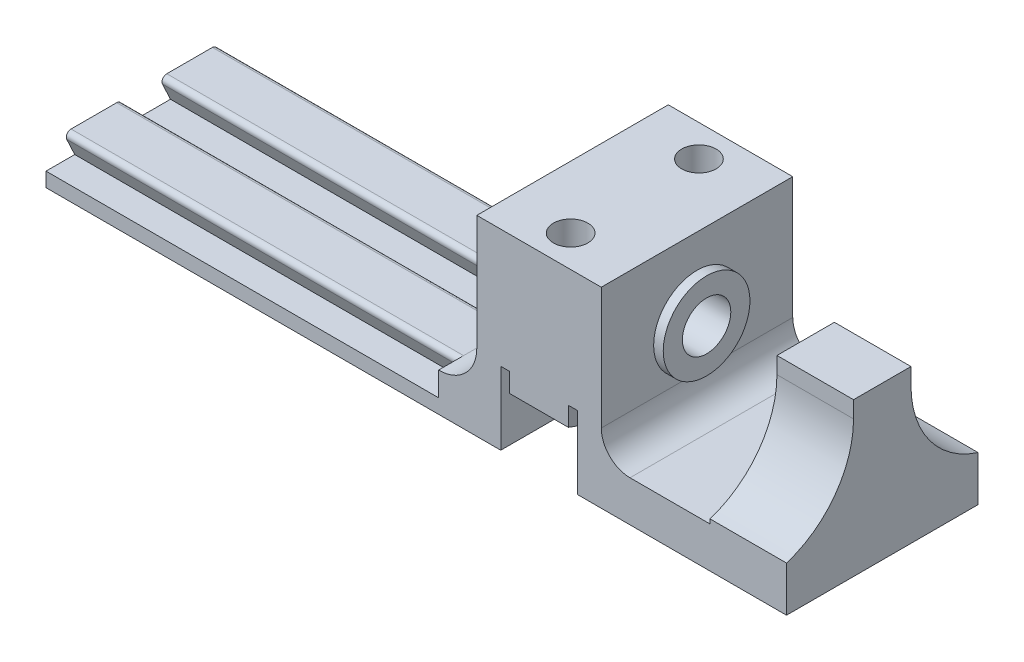
SolidWorks part; units mm, degrees
ref_plane "Front Plane" through (0, 0, 0) normal (0, 0, 1) x (1, 0, 0)
ref_plane "Top Plane" through (0, 0, 0) normal (0, 1, 0) x (1, 0, 0)
ref_plane "Right Plane" through (0, 0, 0) normal (1, 0, 0) x (0, 0, -1)
sketch "Sketch1" plane through (0, 0, 0) normal (0, 1, 0) x (1, 0, 0)
  line L1 (-29, -40) -> (29, -40)
  line L2 (-29, -40) -> (-29, 40)
  line L3 (-29, 40) -> (29, 40)
  line L4 (29, -40) -> (29, 40)
  line L5 (-29, -40) -> (29, 40) construction
  line L6 (-29, 40) -> (29, -40) construction
  point P0 (0, 0)
  dimension "D1" = 58
  dimension "D2" = 80
extrude "Boss-Extrude1" add sketch "Sketch1" along normal blind 4
sketch "Sketch2" plane through (-29, 0, 0) normal (-1, 0, 0) x (0, 0, 1)
  line L10 (0, 0) -> (0, 4) construction
  line L12 (-40, 4) -> (40, 4) construction
  line L13 (1.8342, 4) -> (-1.8342, 4)
  line L14 (-1.8342, 4) -> (-3, 1.5)
  line L15 (-3, 1.5) -> (3, 1.5)
  line L16 (1.8342, 4) -> (3, 1.5)
  line L17 (40, 4) -> (40, 0) construction
  line L18 (8.1658, 4) -> (11.8342, 4)
  line L19 (11.8342, 4) -> (13, 1.5)
  line L20 (13, 1.5) -> (7, 1.5)
  line L21 (7, 1.5) -> (8.1658, 4)
  line L22 (10, 4) -> (10, 1.5) construction
  line L23 (-10, 4) -> (-10, 1.5) construction
  line L24 (-7, 1.5) -> (-8.1658, 4)
  line L25 (-13, 1.5) -> (-7, 1.5)
  line L26 (-11.8342, 4) -> (-13, 1.5)
  line L27 (-8.1658, 4) -> (-11.8342, 4)
  point P6 (0, 1.5)
  dimension "D1" = 65
  dimension "D2" = 2.5
  dimension "D3" = 6
  dimension "D4" = 20
extrude "Cut-Extrude1" cut sketch "Sketch2" against normal blind 25
sketch "Sketch5" plane through (0, 0, 40) normal (0, 0, 1) x (1, 0, 0)
  line L0 (-4, 4) -> (-29, 4) construction
  line L1 (29, 4) -> (16, 4)
  line L2 (29, 4) -> (29, 20)
  line L3 (29, 20) -> (16, 20)
  line L4 (16, 4) -> (16, 20)
  line L5 (-4, 4) -> (-29, 4) construction
  line L6 (-29, 0) -> (29, 0) construction
  dimension "D1" = 20
  dimension "D2" = 20
extrude "Boss-Extrude3" add sketch "Sketch5" against normal up to surface (80 mm away) up to face at (0, 2, -40)
sketch "Sketch6" plane through (29, 0, 0) normal (1, 0, 0) x (0, 0, -1)
  line L0 (0, 20) -> (0, 4) construction
  line L1 (40, 20) -> (-40, 20) construction
  line L3 (40, 4) -> (-40, 4) construction
  line L4 (40, 4) -> (-40, 4) construction
  circle A0 centre (0, 12) radius 2.53
  dimension "D1" = 5.06
extrude "Cut-Extrude2" cut sketch "Sketch6" against normal through all
sketch "Sketch7" plane through (29, 0, 0) normal (1, 0, 0) x (0, 0, -1)
  circle A0 centre (0, 12) radius 2.53 construction
  circle A1 centre (0, 12) radius 2.53
  circle A2 centre (0, 12) radius 4.53
  dimension "D1" = 2
extrude "Boss-Extrude4" add sketch "Sketch7" along normal blind 1
sketch "Sketch8" plane through (0, 20, 0) normal (0, 1, 0) x (1, 0, 0)
  line L0 (22.5, 40) -> (22.5, -40) construction
  line L1 (16, 40) -> (29, 40) construction
  line L2 (29, -40) -> (16, -40) construction
  line L4 (16, 40) -> (16, -40) construction
  line L5 (16, -6.7) -> (22.5, -6.7) construction
  line L6 (22.5, -6.7) -> (16, 6.7) construction
  line L7 (16, 6.7) -> (22.5, 6.7) construction
  line L8 (22.5, 8.5) -> (29, 8.5) construction
  line L9 (17.9973, 36) -> (22.5, 36) construction
  line L10 (29, 40) -> (29, -40) construction
  line L11 (29, 8.5) -> (29, -8.5) construction
  line L12 (16, 6.7) -> (16, -6.7) construction
  line L13 (29, -8.5) -> (22.5, -8.5) construction
  line L14 (29, 10) -> (16, 10) construction
  line L16 (16, -10) -> (29, -10) construction
  line L17 (22.5, -8.5) -> (22.5, -10) construction
  line L18 (29, -8.5) -> (29, -10) construction
  line L19 (29, -10) -> (29, 8.5) construction
  line L20 (29, 8.5) -> (29, 10) construction
  circle A1 centre (22.5, 6.7) radius 1.8
  circle A2 centre (22.5, -6.7) radius 1.8
  point P14 (16, 0)
  point P15 (16, 0)
  dimension "D1" = 3.6
  dimension "D2" = 1.5
  dimension "D3" = 20
extrude "Cut-Extrude3" cut sketch "Sketch8" against normal through all
sketch "Sketch9" plane through (0, 0, 0) normal (0, -1, 0) x (1, 0, 0)
  line L0 (-29, 40) -> (29, 40) construction
  line L1 (18.5, 40) -> (26.5, 40)
  line L2 (18.5, 40) -> (18.5, -40)
  line L3 (18.5, -40) -> (26.5, -40)
  line L4 (26.5, 40) -> (26.5, -40)
  line L5 (29, -40) -> (-29, -40) construction
  line L6 (22.5, 36) -> (22.5, 40) construction
  line L7 (29, 40) -> (29, -40) construction
  dimension "D1" = 8
extrude "Cut-Extrude4" cut sketch "Sketch9" against normal blind 7.6
sketch "Sketch13" plane through (29, 0, 0) normal (1, 0, 0) x (0, 0, -1)
  line L0 (-40, 0) -> (40, 0) construction
  line L1 (0, 5.8719) -> (0, 12) construction
  line L2 (-3, 0) -> (3, 0)
  line L3 (-3, 0) -> (-3, 4.261)
  line L4 (-3, 4.261) -> (3, 4.261)
  line L5 (3, 0) -> (3, 4.261)
  circle A1 centre (0, 12) radius 7.239 construction
  circle A2 centre (0, 12) radius 7.739 construction
  point P10 (0, 0)
  dimension "D1" = 0.5
  dimension "D2" = 6
extrude "Boss-Extrude6" add sketch "Sketch13" along normal blind 11.35
sketch "Sketch14" plane through (40.35, 0, 0) normal (1, 0, 0) x (0, 0, -1)
  line L0 (3, 0) -> (3, 4.261) construction
  line L1 (-3, 0) -> (3, 0)
  line L2 (-3, 0) -> (-3, 16)
  line L3 (-3, 16) -> (3, 16)
  line L4 (3, 0) -> (3, 16)
  dimension "D1" = 16
extrude "Boss-Extrude7" add sketch "Sketch14" along normal blind 8
sketch "Sketch15" plane through (29, 0, 0) normal (1, 0, 0) x (0, 0, -1)
  line L0 (-40, 0) -> (-3, 0) construction
  line L1 (-20, 0) -> (20, 0)
  line L2 (-20, 0) -> (-20, 4.261)
  line L3 (-20, 4.261) -> (20, 4.261)
  line L4 (20, 0) -> (20, 4.261)
  line L5 (3, 4.261) -> (-3, 4.261) construction
  point P6 (0, 0)
  dimension "D1" = 40
extrude "Boss-Extrude8" add sketch "Sketch15" along normal up to surface (19.35 mm away) up to face at (48.35, 8, 0)
fillet "Fillet1" radius 10 2 edges at (44.35, 4.261, 3) (44.35, 4.261, -3)
fillet "Fillet2" radius 3 1 edges at (29, 4.261, 0)
fillet "Fillet3" radius 3 2 edges at (29, 3.6305, -20) (29, 3.6305, 20)
sketch "Sketch17" plane through (0, 4, 0) normal (0, 1, 0) x (1, 0, 0)
  line L1 (-1, -36) -> (16, -36)
  line L2 (-1, -36) -> (-1, -12)
  line L3 (-1, -12) -> (16, -12)
  line L4 (16, -36) -> (16, -12)
  line L5 (16, 40) -> (16, -40) construction
  line L6 (0, 0) -> (11.9578, 0) construction
  line L7 (-1, 12) -> (16, 12)
  line L8 (16, 36) -> (16, 12)
  line L9 (-1, 36) -> (16, 36)
  line L10 (-1, 36) -> (-1, 12)
  line L11 (-29, -40) -> (16, -40) construction
  line L12 (-4, -11.8342) -> (-4, -8.1658) construction
  dimension "D1" = 4
  dimension "D2" = 12
  dimension "D3" = 3
extrude "Cut-Extrude6" cut sketch "Sketch17" against normal through all
fillet "Fillet4" radius 14 2 edges at (16, 4, -38) (16, 4, 38)
fillet "Fillet5" radius 4 1 edges at (16, 4, 0)
fillet "Fillet6" radius 2 4 edges at (16, 9, 36) (16, 4, 12) (16, 4, -12) (16, 9, -36)
fillet "Fillet7" radius 0.5 6 edges at (-16.5, 4, 11.8342) (-16.5, 4, 8.1658) (-16.5, 4, 1.8342) (-16.5, 4, -1.8342) (-16.5, 4, -8.1658) (-16.5, 4, -11.8342)
sketch "Sketch18" plane through (0, 7.6, 0) normal (0, -1, 0) x (1, 0, 0)
  line L0 (20.8828, 38.8011) -> (24.1172, 38.8011)
  line L1 (24.1172, 38.8011) -> (25.7344, 36)
  line L2 (25.7344, 36) -> (24.1172, 33.1989)
  line L3 (24.1172, 33.1989) -> (20.8828, 33.1989)
  line L4 (20.8828, 33.1989) -> (19.2656, 36)
  line L5 (19.2656, 36) -> (20.8828, 38.8011)
  line L6 (20.8828, 38.8011) -> (20.8828, 33.1989) construction
  line L7 (20.8828, 33.1989) -> (25.7344, 36) construction
  line L8 (19.2656, 36) -> (25.7344, 36) construction
  line L9 (20.8828, 9.5011) -> (24.1172, 9.5011)
  line L10 (24.1172, 9.5011) -> (25.7344, 6.7)
  line L11 (25.7344, 6.7) -> (24.1172, 3.8989)
  line L12 (24.1172, 3.8989) -> (20.8828, 3.8989)
  line L13 (20.8828, 3.8989) -> (19.2656, 6.7)
  line L14 (19.2656, 6.7) -> (20.8828, 9.5011)
  line L15 (20.8828, 9.5011) -> (20.8828, 3.8989) construction
  line L16 (20.8828, 3.8989) -> (25.7344, 6.7) construction
  line L17 (19.2656, 6.7) -> (25.7344, 6.7) construction
  line L18 (20.8828, -3.8989) -> (24.1172, -3.8989)
  line L19 (24.1172, -3.8989) -> (25.7344, -6.7)
  line L20 (25.7344, -6.7) -> (24.1172, -9.5011)
  line L21 (24.1172, -9.5011) -> (20.8828, -9.5011)
  line L22 (20.8828, -9.5011) -> (19.2656, -6.7)
  line L23 (19.2656, -6.7) -> (20.8828, -3.8989)
  line L24 (20.8828, -3.8989) -> (20.8828, -9.5011) construction
  line L25 (20.8828, -9.5011) -> (25.7344, -6.7) construction
  line L26 (19.2656, -6.7) -> (25.7344, -6.7) construction
  line L27 (20.8828, -33.1989) -> (24.1172, -33.1989)
  line L28 (24.1172, -33.1989) -> (25.7344, -36)
  line L29 (25.7344, -36) -> (24.1172, -38.8011)
  line L30 (24.1172, -38.8011) -> (20.8828, -38.8011)
  line L31 (20.8828, -38.8011) -> (19.2656, -36)
  line L32 (19.2656, -36) -> (20.8828, -33.1989)
  line L33 (20.8828, -33.1989) -> (20.8828, -38.8011) construction
  line L34 (20.8828, -38.8011) -> (25.7344, -36) construction
  line L35 (19.2656, -36) -> (25.7344, -36) construction
  line L36 (20.0168, 40.3011) -> (24.9832, 40.3011)
  line L37 (24.9832, 40.3011) -> (27.4665, 36)
  line L38 (27.4665, 36) -> (24.9832, 31.6989)
  line L39 (24.9832, 31.6989) -> (20.0168, 31.6989)
  line L40 (20.0168, 31.6989) -> (17.5335, 36)
  line L41 (17.5335, 36) -> (20.0168, 40.3011)
  line L42 (20.0168, 11.0011) -> (24.9832, 11.0011)
  line L43 (24.9832, 11.0011) -> (27.4665, 6.7)
  line L44 (27.4665, 6.7) -> (24.9832, 2.3989)
  line L45 (24.9832, 2.3989) -> (20.0168, 2.3989)
  line L46 (20.0168, 2.3989) -> (17.5335, 6.7)
  line L47 (17.5335, 6.7) -> (20.0168, 11.0011)
  line L48 (20.0168, -2.3989) -> (24.9832, -2.3989)
  line L49 (24.9832, -2.3989) -> (27.4665, -6.7)
  line L50 (27.4665, -6.7) -> (24.9832, -11.0011)
  line L51 (24.9832, -11.0011) -> (20.0168, -11.0011)
  line L52 (20.0168, -11.0011) -> (17.5335, -6.7)
  line L53 (17.5335, -6.7) -> (20.0168, -2.3989)
  line L54 (20.0168, -31.6989) -> (24.9832, -31.6989)
  line L55 (24.9832, -31.6989) -> (27.4665, -36)
  line L56 (27.4665, -36) -> (24.9832, -40.3011)
  line L57 (24.9832, -40.3011) -> (20.0168, -40.3011)
  line L58 (20.0168, -40.3011) -> (17.5335, -36)
  line L59 (17.5335, -36) -> (20.0168, -31.6989)
  circle A0 centre (22.5, 36) radius 1.8 construction
  circle A1 centre (22.5, -6.7) radius 1.8 construction
  circle A2 centre (22.5, -6.7) radius 1.8 construction
  circle A3 centre (22.5, 6.7) radius 1.8 construction
  circle A4 centre (22.5, -36) radius 1.8 construction
  circle A5 centre (22.5, 6.7) radius 1.8 construction
  circle A6 centre (22.5, -36) radius 1.8 construction
  circle A7 centre (22.5, 36) radius 1.8 construction
  circle A8 centre (22.5, 36) radius 1.8 construction
  circle A9 centre (22.5, 6.7) radius 6.0752 construction
  circle A10 centre (22.5, -6.7) radius 5.0746 construction
  circle A11 centre (22.5, -36) radius 1.8 construction
  point P8 (22.5, 36)
  point P30 (22.5, 6.7)
  point P39 (22.5, -6.7)
  point P48 (22.5, -36)
  dimension "D1" = 3.2344
  dimension "D2" = 1.5
  dimension "D3" = 1.5
  dimension "D4" = 1.5
  dimension "D5" = 1.5
extrude "Boss-Extrude10" add sketch "Sketch18" along normal blind 2
sketch "Sketch19" plane through (0, 0, 0) normal (0, -1, 0) x (1, 0, 0)
  line L0 (29, 40) -> (29, 23) construction
  line L1 (29, -40) -> (-29, -40)
  line L2 (29, -40) -> (29, -45.5715)
  line L3 (29, -45.5715) -> (-29, -45.5715)
  line L4 (-29, -40) -> (-29, -45.5715)
  line L5 (-29, 40) -> (29, 40)
  line L6 (-29, 40) -> (-29, 54.101)
  line L7 (-29, 54.101) -> (29, 54.101)
  line L8 (29, 40) -> (29, 54.101)
extrude "Cut-Extrude7" cut sketch "Sketch19" against normal through all
sketch "Sketch20" plane through (0, 20, 0) normal (0, 1, 0) x (1, 0, 0)
  line L1 (-48.35, -10) -> (48.35, -10) construction
  line L2 (-48.35, -10) -> (-48.35, 10) construction
  line L3 (-48.35, 10) -> (48.35, 10) construction
  line L4 (48.35, -10) -> (48.35, 10) construction
  line L5 (-48.35, -10) -> (48.35, 10) construction
  line L6 (-48.35, 10) -> (48.35, -10) construction
  line L7 (48.35, 13) -> (48.35, 20) construction
  line L8 (29, 10) -> (16, 10) construction
  line L9 (16, 40) -> (29, 40) construction
  line L10 (-48.35, 10) -> (48.35, 10)
  line L11 (-48.35, 10) -> (-48.35, 40)
  line L12 (-48.35, 40) -> (48.35, 40)
  line L13 (48.35, 10) -> (48.35, 40)
  line L14 (29, -40) -> (16, -40) construction
  line L15 (-48.35, -10) -> (48.35, -10)
  line L16 (-48.35, -10) -> (-48.35, -40)
  line L17 (-48.35, -40) -> (48.35, -40)
  line L18 (48.35, -10) -> (48.35, -40)
  point P0 (0, 0)
extrude "Cut-Extrude8" cut sketch "Sketch20" against normal through all
sketch "Sketch22" plane through (-4, 0, 0) normal (-1, 0, 0) x (0, 0, 1)
  line L0 (-10, 4) -> (-10, 1.5) construction
  line L1 (-10, 1.5) -> (-7, 1.5) construction
  line L2 (-7, 1.5) -> (-7.8341, 3.2887) construction
  line L3 (-7.3809, 4) -> (-10, 4) construction
  line L4 (3, 1.5) -> (2.1659, 3.2887) construction
  line L5 (2.6191, 4) -> (-2.6191, 4) construction
  line L6 (-2.1659, 3.2887) -> (-3, 1.5) construction
  line L7 (-3, 1.5) -> (3, 1.5) construction
  line L8 (7, 1.5) -> (10, 1.5) construction
  line L9 (10, 1.5) -> (10, 4) construction
  line L10 (10, 4) -> (7.3809, 4) construction
  line L11 (7.8341, 3.2887) -> (7, 1.5) construction
  line L12 (-10, 4) -> (-10, 1.5)
  line L13 (-10, 1.5) -> (-7, 1.5)
  line L14 (-7, 1.5) -> (-7.8341, 3.2887)
  line L15 (-7.3809, 4) -> (-10, 4)
  line L16 (3, 1.5) -> (2.1659, 3.2887)
  line L17 (2.6191, 4) -> (-2.6191, 4)
  line L18 (-2.1659, 3.2887) -> (-3, 1.5)
  line L19 (-3, 1.5) -> (3, 1.5)
  line L20 (7, 1.5) -> (10, 1.5)
  line L21 (10, 1.5) -> (10, 4)
  line L22 (10, 4) -> (7.3809, 4)
  line L23 (7.8341, 3.2887) -> (7, 1.5)
  arc A0 (-7.3809, 4) -> (-7.8341, 3.2887) centre (-7.3809, 3.5) ccw construction
  arc A1 (2.6191, 4) -> (2.1659, 3.2887) centre (2.6191, 3.5) ccw construction
  arc A2 (-2.1659, 3.2887) -> (-2.6191, 4) centre (-2.6191, 3.5) ccw construction
  arc A3 (7.8341, 3.2887) -> (7.3809, 4) centre (7.3809, 3.5) ccw construction
  arc A4 (-7.3809, 4) -> (-7.8341, 3.2887) centre (-7.3809, 3.5) ccw
  arc A5 (2.6191, 4) -> (2.1659, 3.2887) centre (2.6191, 3.5) ccw
  arc A6 (-2.1659, 3.2887) -> (-2.6191, 4) centre (-2.6191, 3.5) ccw
  arc A7 (7.8341, 3.2887) -> (7.3809, 4) centre (7.3809, 3.5) ccw
extrude "Cut-Extrude9" cut sketch "Sketch22" against normal up to vertex (16 mm away) up to point (12, 4, 10)
